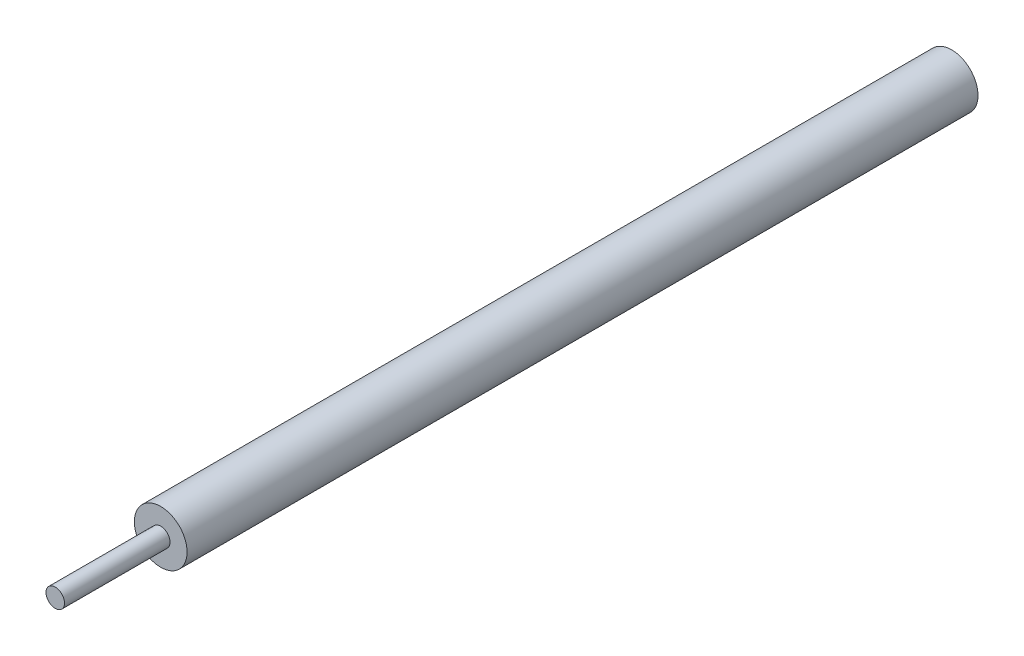
SolidWorks part; units mm, degrees
ref_plane "Front Plane" through (0, 0, 0) normal (0, 0, 1) x (1, 0, 0)
ref_plane "Top Plane" through (0, 0, 0) normal (0, 1, 0) x (1, 0, 0)
ref_plane "Right Plane" through (0, 0, 0) normal (1, 0, 0) x (0, 0, -1)
sketch "Sketch1" plane through (0, 0, 0) normal (0, 0, 1) x (1, 0, 0)
  circle A0 centre (0, 0) radius 5
extrude "Boss-Extrude1" add sketch "Sketch1" along normal blind 150
sketch "Sketch2" plane through (0, 0, 150) normal (0, 0, 1) x (1, 0, 0)
  circle A0 centre (0, 0) radius 1.7592
extrude "Boss-Extrude2" add sketch "Sketch2" along normal blind 20
